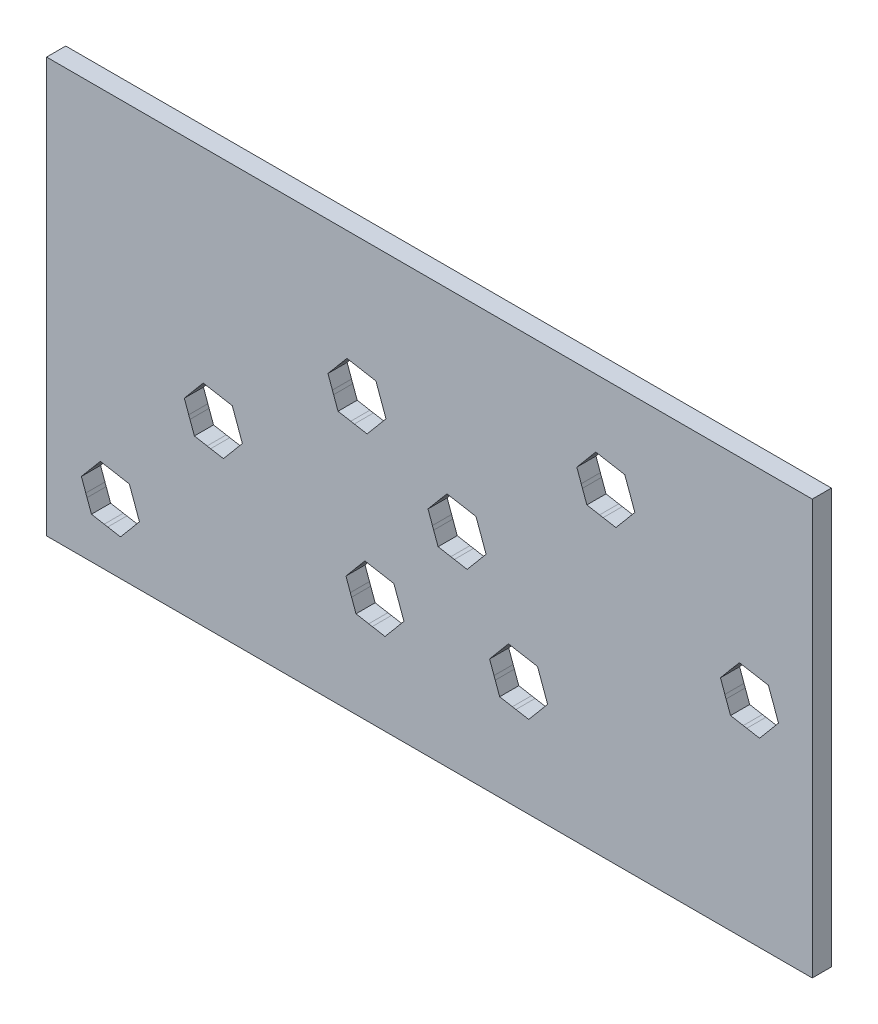
SolidWorks part; units mm, degrees
material "7075-T6, Platte (SS)"
ref_plane "Ebene vorne" through (0, 0, 0) normal (0, 0, 1) x (1, 0, 0)
ref_plane "Ebene oben" through (0, 0, 0) normal (0, 1, 0) x (1, 0, 0)
ref_plane "Ebene rechts" through (0, 0, 0) normal (1, 0, 0) x (0, 0, -1)
sketch "Skizze1" plane through (0, 0, 0) normal (0, 0, 1) x (1, 0, 0)
  line L1 (0, 0) -> (120, 0)
  line L2 (0, 0) -> (0, 65)
  line L3 (0, 65) -> (120, 65)
  line L4 (120, 0) -> (120, 65)
  dimension "D1" = 120
  dimension "D2" = 65
extrude "Aufsatz-Linear austragen1" add sketch "Skizze1" along normal blind 3
sketch "Skizze2" plane through (0, 0, 3) normal (0, 0, 1) x (1, 0, 0)
  line L0 (0, 0) -> (120, 0) construction
  line L1 (12.9689, 13.5382) -> (8.4203, 14.3403)
  line L2 (8.4203, 14.3403) -> (5.4514, 10.802)
  line L3 (5.4514, 10.802) -> (7.0311, 6.4618)
  line L4 (7.0311, 6.4618) -> (11.5797, 5.6597)
  line L5 (11.5797, 5.6597) -> (14.5486, 9.198)
  line L6 (14.5486, 9.198) -> (12.9689, 13.5382)
  line L7 (0, 0) -> (0, 65) construction
  line L8 (0, 65) -> (0, 0) construction
  circle A0 centre (10, 10) radius 4 construction
  dimension "D1" = 8
  dimension "D2" = 10
  dimension "D3" = 10
  dimension "D4" = 80
extrude "Sechskant" cut sketch "Skizze2" against normal through all
sketch "Skizze3" plane through (0, 0, 3) normal (0, 0, 1) x (1, 0, 0)
  circle A0 centre (10, 10) radius 4.01
  circle A1 centre (10, 10) radius 4 construction
  dimension "D1" = 0.01
extrude "Zylinderbohrung" cut sketch "Skizze3" against normal through all
sketch "Skizze4" plane through (0, 0, 3) normal (0, 0, 1) x (1, 0, 0)
  point P0 (26.1314, 28.6885)
  point P1 (48.6464, 43.2989)
  point P2 (73.9758, 17.2149)
  point P3 (87.6456, 50.0867)
  point P4 (110.1606, 32.7546)
  point P5 (51.4608, 17.2149)
  point P6 (64.3265, 32.7546)
pattern_sketch "Skizzen-Muster1" of "Sechskant", "Zylinderbohrung" driven by "Skizze4"
